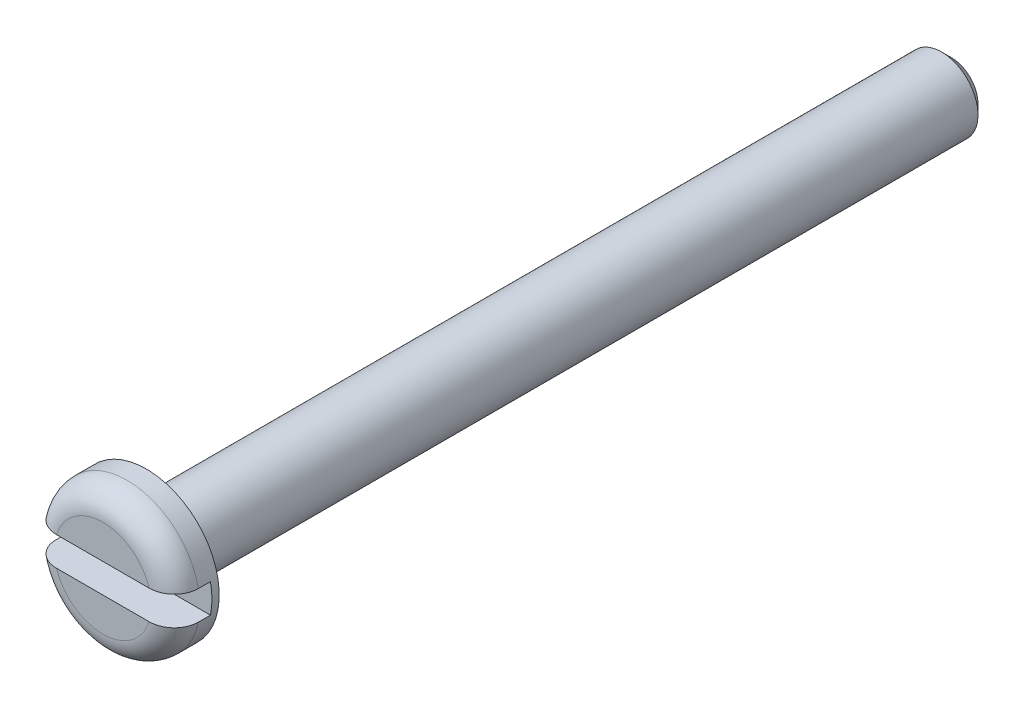
SolidWorks part; units mm, degrees
material "Простая углеродистая сталь"
ref_plane "Спереди" through (0, 0, 0) normal (0, 0, 1) x (1, 0, 0)
ref_plane "Сверху" through (0, 0, 0) normal (0, 1, 0) x (1, 0, 0)
ref_plane "Справа" through (0, 0, 0) normal (1, 0, 0) x (0, 0, -1)
sketch "Эскиз1" plane through (0, 0, 0) normal (0, 1, 0) x (1, 0, 0)
  line L0 (0, 0) -> (-3, 0)
  line L1 (-3, 0) -> (-3, 1.8)
  line L2 (-3, 1.8) -> (-1.5, 1.8)
  line L3 (-1.5, 1.8) -> (-1.5, 35)
  line L4 (-1.5, 35) -> (0, 35)
  line L5 (0, 35) -> (0, 0)
  dimension "D1" = 3
  dimension "D2" = 1.8
  dimension "D3" = 35
  dimension "D4" = 1.5
revolve "Повернуть1" add sketch "Эскиз1" angle 360 about L5
sketch "Эскиз2" plane through (0, 0, 0) normal (1, 0, 0) x (0, 0, -1)
  line L0 (0, 0) -> (22.6818, 0) construction
  line L1 (0, -0.6) -> (0, 0.6)
  line L2 (0, 0.6) -> (1.5, 0.6)
  line L3 (0, -0.6) -> (1.5, -0.6)
  line L4 (1.5, 0.6) -> (1.5, -0.6)
  point P7 (0, 0)
  point P10 (1.5, 0)
  dimension "D1" = 1.2
  dimension "D2" = 1.5
extrude "Вырез-Вытянуть1" cut sketch "Эскиз2" against normal through all both and the other way through all
chamfer "Фаска1" distance 0.4 angle 45 1 edges at (-1.5, 0, -35)
fillet "Скругление1" radius 1 2 edges at (0, -3, 0) (0, 3, 0)
fillet "Скругление2" radius 0.4 1 edges at (-1.5, 0, -1.8)
